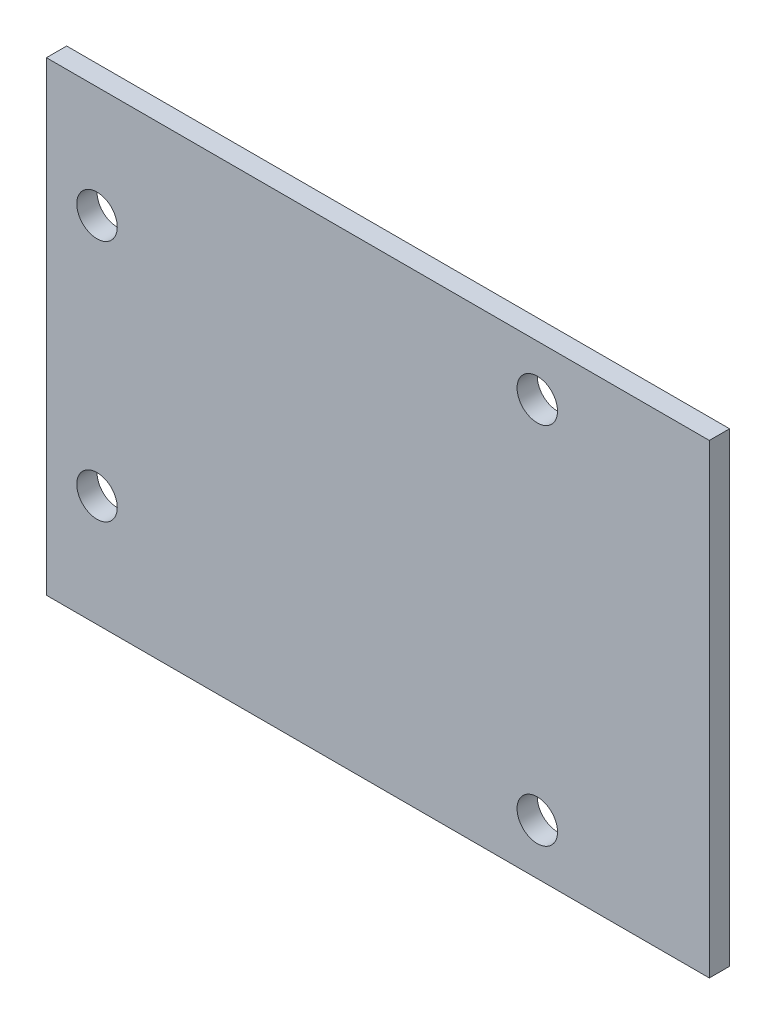
SolidWorks part; units mm, degrees
ref_plane "Plan de face" through (0, 0, 0) normal (0, 0, 1) x (1, 0, 0)
ref_plane "Plan de dessus" through (0, 0, 0) normal (0, 1, 0) x (1, 0, 0)
ref_plane "Plan de droite" through (0, 0, 0) normal (1, 0, 0) x (0, 0, -1)
sketch "Esquisse1" plane through (0, 0, 0) normal (0, 0, 1) x (1, 0, 0)
  line L1 (0, 0) -> (65.5, 0)
  line L2 (0, 0) -> (0, 46)
  line L3 (0, 46) -> (65.5, 46)
  line L4 (65.5, 0) -> (65.5, 46)
  dimension "D1" = 46
  dimension "D2" = 65.5
extrude "Boss.-Extru.1" add sketch "Esquisse1" along normal blind 2
sketch "Esquisse2" plane through (0, 0, 2) normal (0, 0, 1) x (1, 0, 0)
  line L1 (0, 0) -> (65.5, 0) construction
  line L2 (65.5, 46) -> (0, 46) construction
  line L3 (0, 46) -> (0, 0) construction
  circle A0 centre (5, 11) radius 2
  circle A1 centre (5, 35) radius 2
  circle A2 centre (48.5, 41) radius 2
  circle A3 centre (48.5, 5) radius 2
  dimension "D1" = 4
  dimension "D2" = 48.5
  dimension "D3" = 5
  dimension "D4" = 11
  dimension "D5" = 11
  dimension "D6" = 5
  dimension "D7" = 5
  dimension "D8" = 24
  dimension "D9" = 36
extrude "Enlèv. mat.-Extru.1" cut sketch "Esquisse2" against normal through all
